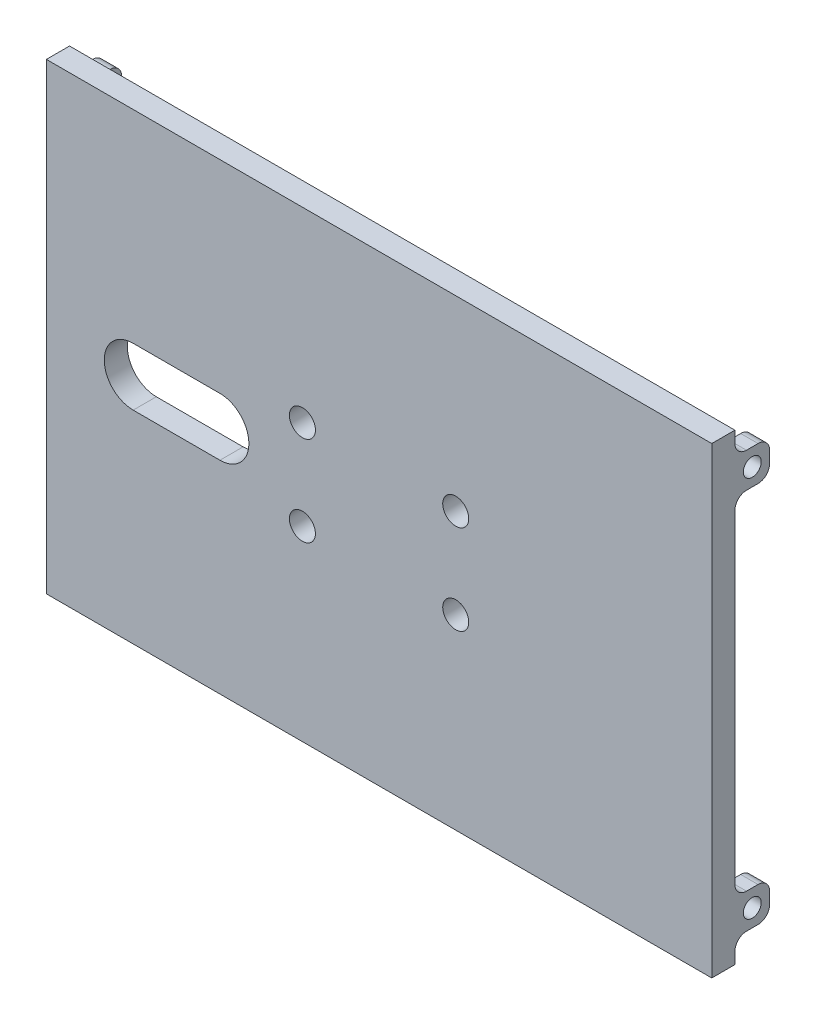
SolidWorks part; units mm, degrees
ref_plane "Front Plane" through (0, 0, 0) normal (1, 0, 0) x (0, 1, 0)
ref_plane "Top Plane" through (0, 0, 0) normal (0, 0, 1) x (0, 1, 0)
ref_plane "Right Plane" through (0, 0, 0) normal (0, 1, 0) x (-1, 0, 0)
sketch "Sketch1" plane through (0, 0, 0) normal (0, 0, 1) x (0, 1, 0)
  line L1 (-40, -57.5) -> (40, -57.5)
  line L2 (-40, -57.5) -> (-40, 57.5)
  line L3 (-40, 57.5) -> (40, 57.5)
  line L4 (40, -57.5) -> (40, 57.5)
  line L5 (-40, -57.5) -> (40, 57.5) construction
  line L6 (-40, 57.5) -> (40, -57.5) construction
  point P0 (0, 0)
  dimension "D1" = 115
  dimension "D2" = 80
extrude "Boss-Extrude1" add sketch "Sketch1" along normal blind 4
sketch "Sketch2" plane through (0, 0, 4) normal (0, 0, 1) x (1, 0, 0)
  line L0 (0, 0) -> (0, 40) construction
  line L1 (57.5, 40) -> (-57.5, 40) construction
  line L2 (0, 0) -> (57.5, 0) construction
  line L3 (57.5, -40) -> (57.5, 40) construction
  circle A0 centre (13.25, 7.75) radius 2.25
  circle A1 centre (-13.25, 7.75) radius 2.25
  circle A2 centre (13.25, -7.75) radius 2.25
  circle A3 centre (-13.25, -7.75) radius 2.25
  dimension "D1" = 4.5
  dimension "D2" = 7.75
  dimension "D3" = 13.25
extrude "Cut-Extrude1" cut sketch "Sketch2" against normal up to next
sketch "Sketch4" plane through (0, 0, 0) normal (0, 0, -1) x (1, 0, 0)
  line L0 (0, 0) -> (0, 40) construction
  line L1 (-57.5, 40) -> (57.5, 40) construction
  line L2 (0, 0) -> (57.5, 0) construction
  line L3 (57.5, 40) -> (57.5, -40) construction
  line L4 (-57.5, 36) -> (-54.5, 36)
  line L5 (57.5, 30) -> (54.5, 30)
  line L6 (57.5, 30) -> (57.5, 36)
  line L7 (57.5, 36) -> (54.5, 36)
  line L8 (54.5, 30) -> (54.5, 36)
  line L9 (-54.5, 30) -> (-54.5, 36)
  line L10 (-57.5, 30) -> (-54.5, 30)
  line L11 (-57.5, 30) -> (-57.5, 36)
  line L12 (-57.5, -30) -> (-57.5, -36)
  line L13 (-57.5, -30) -> (-54.5, -30)
  line L14 (-54.5, -30) -> (-54.5, -36)
  line L15 (-57.5, -36) -> (-54.5, -36)
  line L16 (57.5, -36) -> (54.5, -36)
  line L17 (54.5, -30) -> (54.5, -36)
  line L18 (57.5, -30) -> (54.5, -30)
  line L19 (57.5, -30) -> (57.5, -36)
  dimension "D1" = 3
  dimension "D2" = 6
  dimension "D3" = 30
extrude "Boss-Extrude3" add sketch "Sketch4" along normal blind 6
sketch "Sketch5" plane through (57.5, 0, 0) normal (1, 0, 0) x (0, 1, 0)
  line L2 (-36, -3) -> (-30, -3) construction
  line L3 (-36, -6) -> (-36, 0) construction
  line L4 (-30, -6) -> (-30, 0) construction
  line L5 (0, 4) -> (0, 0) construction
  line L6 (-40, 4) -> (40, 4) construction
  circle A0 centre (-33, -3) radius 1.55
  circle A1 centre (33, -3) radius 1.55
  dimension "D1" = 3.1
extrude "Cut-Extrude2" cut sketch "Sketch5" against normal through all both and the other way through all
fillet "Fillet1" radius 2 16 edges at (-56, 30, 0) (-56, 36, 0) (-56, 36, -6) (-56, 30, -6) (-56, -30, 0) (-56, -30, -6) (-56, -36, -6) (-56, -36, 0) (56, 30, 0) (56, 30, -6) (56, 36, -6) (56, 36, 0) (56, -30, 0) (56, -30, -6) (56, -36, -6) (56, -36, 0)
sketch "Sketch6" plane through (0, 0, 0) normal (0, 0, -1) x (1, 0, 0)
  line L0 (-57.5, 0) -> (0, 0) construction
  line L1 (-57.5, -28) -> (-57.5, 28) construction
  line L2 (-42.5, 0) -> (-27.5, 0) construction
  line L3 (-42.5, 5) -> (-27.5, 5)
  line L4 (-42.5, -5) -> (-27.5, -5)
  arc A0 (-42.5, 5) -> (-42.5, -5) centre (-42.5, 0) ccw
  arc A1 (-27.5, -5) -> (-27.5, 5) centre (-27.5, 0) ccw
  point P7 (-35, 0)
  dimension "D2" = 5
  dimension "D1" = 15
  dimension "D3" = 35
extrude "Cut-Extrude3" cut sketch "Sketch6" against normal up to next
